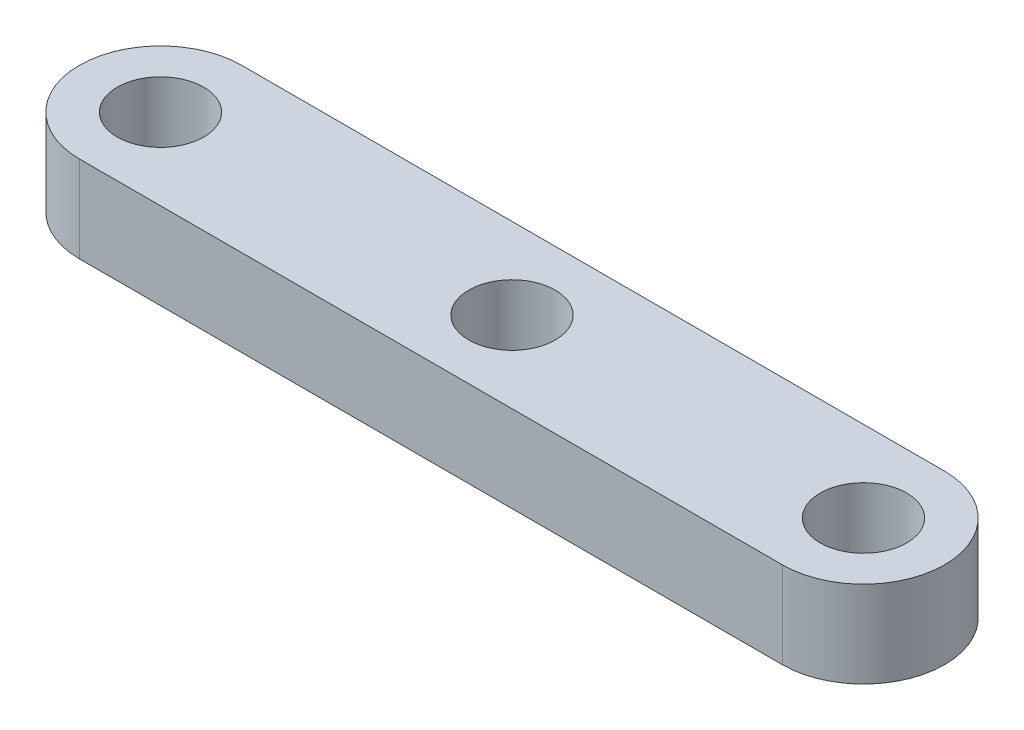
SolidWorks part; units mm, degrees
ref_plane "Front Plane" through (0, 0, 0) normal (0, 0, 1) x (1, 0, 0)
ref_plane "Top Plane" through (0, 0, 0) normal (0, 1, 0) x (1, 0, 0)
ref_plane "Right Plane" through (0, 0, 0) normal (1, 0, 0) x (0, 0, -1)
sketch "Sketch1" plane through (0, 0, 0) normal (0, 1, 0) x (1, 0, 0)
  line L0 (0, 0) -> (32.5, 0) construction
  line L1 (0, 3.75) -> (32.5, 3.75)
  line L2 (0, -3.75) -> (32.5, -3.75)
  line L3 (-2, 0) -> (-3.75, 0) construction
  line L4 (34.5, 0) -> (36.25, 0) construction
  arc A0 (0, 3.75) -> (0, -3.75) centre (0, 0) ccw
  arc A1 (32.5, -3.75) -> (32.5, 3.75) centre (32.5, 0) ccw
  circle A2 centre (0, 0) radius 2
  circle A3 centre (16.25, 0) radius 2
  circle A4 centre (32.5, 0) radius 2
  point P3 (16.25, 0)
  dimension "D1" = 4
  dimension "D2" = 40
  dimension "D3" = 7.5
extrude "Boss-Extrude1" add sketch "Sketch1" along normal blind 4
